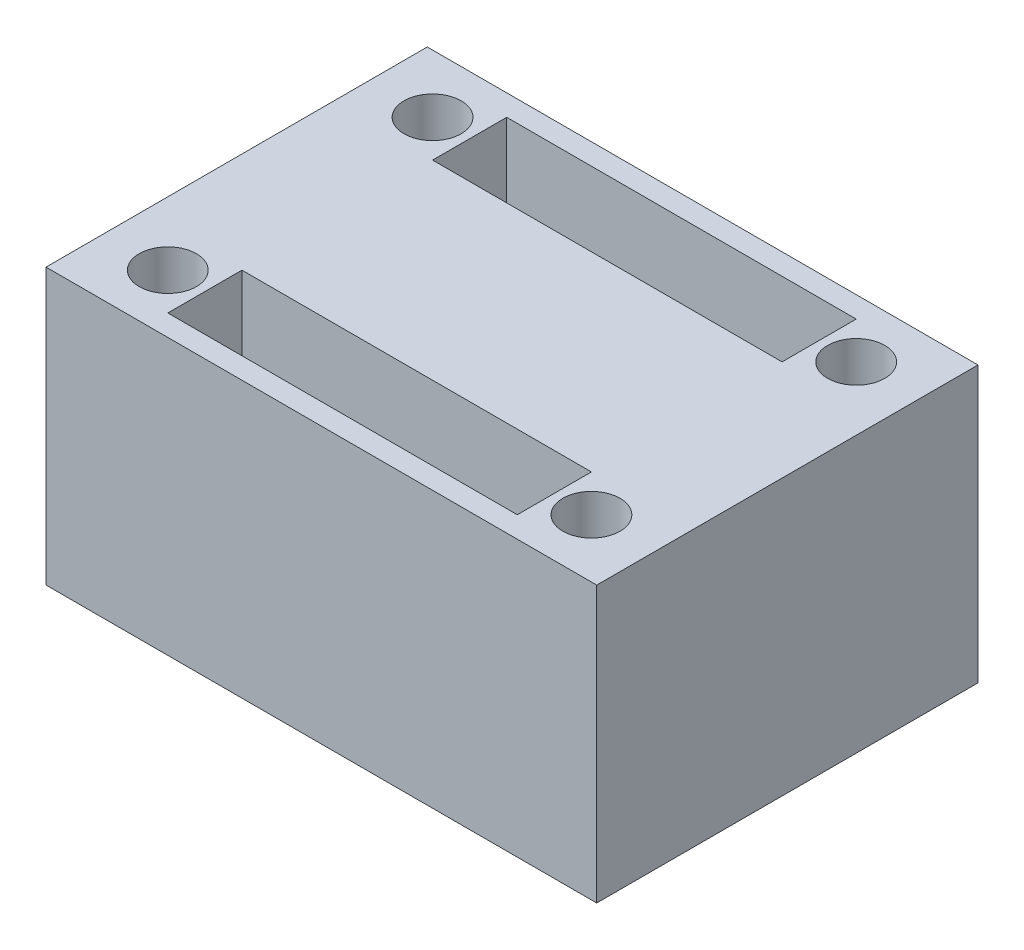
SolidWorks part; units mm, degrees
ref_plane "Front Plane" through (0, 0, 0) normal (0, 0, 1) x (1, 0, 0)
ref_plane "Top Plane" through (0, 0, 0) normal (0, 1, 0) x (1, 0, 0)
ref_plane "Right Plane" through (0, 0, 0) normal (1, 0, 0) x (0, 0, -1)
sketch "Sketch1" plane through (0, 0, 0) normal (0, 1, 0) x (1, 0, 0)
  line L1 (0, 0) -> (26, 0)
  line L2 (0, 0) -> (0, 18)
  line L3 (0, 18) -> (26, 18)
  line L4 (26, 0) -> (26, 18)
  dimension "D1" = 18
  dimension "D2" = 26
extrude "Boss-Extrude1" add sketch "Sketch1" along normal blind 13
sketch "Sketch2" plane through (0, 13, 0) normal (0, 1, 0) x (1, 0, 0)
  line L0 (13, 18) -> (13, 0) construction
  line L1 (3, 15.25) -> (23, 15.25) construction
  line L2 (3, 15.25) -> (3, 2.75) construction
  line L3 (3, 2.75) -> (23, 2.75) construction
  line L4 (23, 15.25) -> (23, 2.75) construction
  line L5 (26, 18) -> (0, 18) construction
  line L6 (0, 0) -> (26, 0) construction
  line L7 (0, 9) -> (26, 9) construction
  line L8 (0, 18) -> (0, 0) construction
  line L9 (26, 0) -> (26, 18) construction
  line L10 (21.25, 13.5) -> (21.25, 17)
  line L11 (4.75, 4.5) -> (21.25, 4.5)
  line L12 (4.75, 4.5) -> (4.75, 1)
  line L13 (4.75, 1) -> (21.25, 1)
  line L14 (21.25, 4.5) -> (21.25, 1)
  line L15 (4.75, 17) -> (21.25, 17)
  line L16 (4.75, 13.5) -> (4.75, 17)
  line L17 (4.75, 13.5) -> (21.25, 13.5)
  circle A0 centre (3, 15.25) radius 1.35
  circle A1 centre (23, 15.25) radius 1.35
  circle A2 centre (3, 2.75) radius 1.35
  circle A3 centre (23, 2.75) radius 1.35
  point P16 (3, 9)
  point P17 (13, 15.25)
  point P26 (4.75, 2.75)
  point P27 (13, 4.5)
  dimension "D3" = 2.7
  dimension "D1" = 20
  dimension "D2" = 12.5
  dimension "D4" = 16.5
  dimension "D5" = 3.5
extrude "Cut-Extrude1" cut sketch "Sketch2" against normal through all
